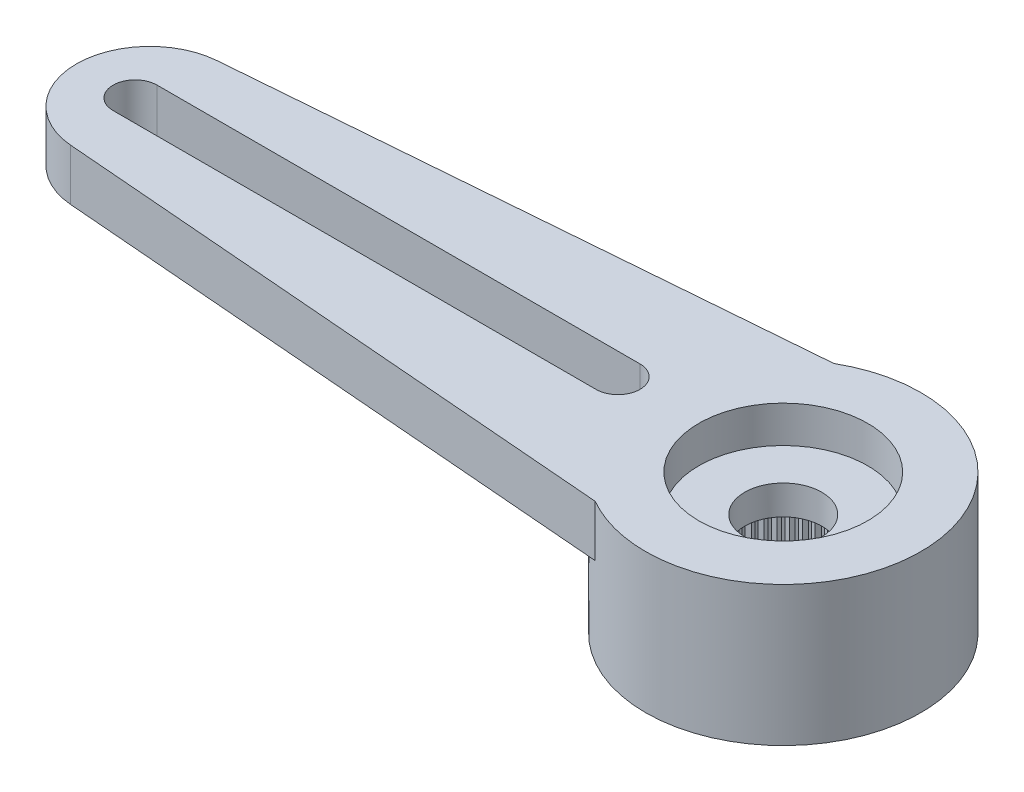
SolidWorks part; units mm, degrees
material "PVC Rígido"
ref_plane "Plano frontal" through (0, 0, 0) normal (0, 0, 1) x (1, 0, 0)
ref_plane "Plano superior" through (0, 0, 0) normal (0, 1, 0) x (1, 0, 0)
ref_plane "Plano direito" through (0, 0, 0) normal (1, 0, 0) x (0, 0, -1)
sketch "Esboço1" plane through (0, 0, 0) normal (0, 1, 0) x (1, 0, 0)
  line L0 (0, 0) -> (-17.25, 0) construction
  line L1 (-17.4112, 1.9935) -> (-1.8708, 3.25)
  line L2 (-1.8708, -3.25) -> (-17.4112, -1.9935)
  arc A0 (-1.8708, -3.25) -> (-1.8708, 3.25) centre (0, 0) ccw
  arc A1 (-17.4112, 1.9935) -> (-17.4112, -1.9935) centre (-17.25, 0) ccw
  dimension "D1" = 7.5
  dimension "D2" = 4
  dimension "D3" = 23
  dimension "D4" = 6.5
extrude "Ressalto-extrusão1" add sketch "Esboço1" against normal blind 1.4
sketch "Esboço2" plane through (0, -1.4, 0) normal (0, -1, 0) x (1, 0, 0)
  arc A0 (-1.8708, -3.25) -> (-1.8708, 3.25) centre (0, 0) ccw construction
  circle A1 centre (0, 0) radius 3.75
extrude "Ressalto-extrusão2" add sketch "Esboço2" along normal offset from surface (2.4 mm away) 3.8 up to face at (-8.6955, 0, 0)
hole_wizard "Furo4" positions "Esboço9" profile "Esboço10" legacy end condition through all
sketch "Esboço9" plane through (0, 0, 0) normal (0, 1, 0) x (1, 0, 0)
  line L1 (-17.65, 0) -> (0, 0) construction
  arc A2 (-17.4112, 1.9935) -> (-17.4112, -1.9935) centre (-17.25, 0) ccw construction
  point P0 (-17.65, 0)
  point P19 (-19.25, 0)
  dimension "D1" = 1.6
sketch "Esboço10" plane through (-17.65, 0, 0) normal (1, 0, 0) x (0, 0, 1)
  line L0 (0, 0) -> (0, 3.8)
  line L1 (0, 3.8) -> (0.6, 3.8)
  line L2 (0.6, 3.8) -> (0.6, 0)
  line L3 (0.6, 0) -> (0, 0)
  line L4 (0, 110) -> (0, -10) construction
  dimension "Diameter" = 1.2
  dimension "Depth" = 3.8
hole_wizard "Furo1" positions "Esboço3" profile "Esboço4" legacy
sketch "Esboço3" plane through (0, -3.8, 0) normal (0, -1, 0) x (-1, 0, 0)
  point P0 (0, 0)
sketch "Esboço4" plane through (0, -3.8, 0) normal (1, 0, 0) x (0, 0, -1)
  line L0 (0, 0) -> (0, 2)
  line L1 (0, 2) -> (2.475, 2)
  line L2 (2.475, 2) -> (2.475, 0)
  line L3 (2.475, 0) -> (0, 0)
  line L4 (0, 110) -> (0, -10) construction
  dimension "Diameter" = 4.95
  dimension "Depth" = 2
hole_wizard "Furo2" positions "Esboço5" profile "Esboço6" legacy
sketch "Esboço5" plane through (0, 0, 0) normal (0, 1, 0) x (1, 0, 0)
  point P0 (0, 0)
sketch "Esboço6" plane through (0, 0, 0) normal (1, 0, 0) x (0, 0, 1)
  line L0 (0, 0) -> (0, 1)
  line L1 (0, 1) -> (2.3, 1)
  line L2 (2.3, 1) -> (2.3, 0)
  line L3 (2.3, 0) -> (0, 0)
  line L4 (0, 110) -> (0, -10) construction
  dimension "Diameter" = 4.6
  dimension "Depth" = 1
hole_wizard "Furo3" positions "Esboço7" profile "Esboço8" legacy end condition through all
sketch "Esboço7" plane through (0, 0, 0) normal (0, 1, 0) x (1, 0, 0)
  point P0 (0, 0)
sketch "Esboço8" plane through (0, 0, 0) normal (1, 0, 0) x (0, 0, 1)
  line L0 (0, 0) -> (0, 3.8)
  line L1 (0, 3.8) -> (1.05, 3.8)
  line L2 (1.05, 3.8) -> (1.05, 0)
  line L3 (1.05, 0) -> (0, 0)
  line L4 (0, 110) -> (0, -10) construction
  dimension "Diameter" = 2.1
  dimension "Depth" = 3.8
sketch "Esboço11" plane through (0, -3.8, 0) normal (0, -1, 0) x (1, 0, 0)
  line L0 (-0.0981, 2.4731) -> (0, 2.375)
  line L1 (0, 2.375) -> (0.0981, 2.4731)
  line L2 (0, 0) -> (0, 2.475) construction
  circle A0 centre (0, 0) radius 2.375 construction
  circle A1 centre (0, 0) radius 2.475
  arc A2 (0.0981, 2.4731) -> (-0.0981, 2.4731) centre (0, 0) ccw
  dimension "D3" = 4.75
  dimension "D2" = 0.1
  dimension "D1" = 0
extrude "Ressalto-extrusão3" add sketch "Esboço11" against normal up to surface (2 mm away) up to face at (0, -1.8, 1.05)
pattern_circular "PadrãoCircular1" count 60 over 360 about axis through (0, 0, 0) along (0, 1, 0) of "Ressalto-extrusão3"
sketch "Sketch1" plane through (0, 0, 0) normal (0, 1, 0) x (1, 0, 0)
  line L0 (-17.65, 0.6) -> (-4.5, 0.6)
  line L1 (-17.65, -0.6) -> (-4.5, -0.6)
  circle A0 centre (-17.65, 0) radius 0.6 construction
  arc A1 (-17.65, 0.6) -> (-17.65, -0.6) centre (-17.65, 0) ccw
  arc A2 (-4.5, -0.6) -> (-4.5, 0.6) centre (-4.5, 0) ccw
  dimension "D1" = 4.5
extrude "Cut-Extrude1" cut sketch "Sketch1" against normal up to surface (1.4 mm away) up to face at (-17.65, -1.4, 0.6)
